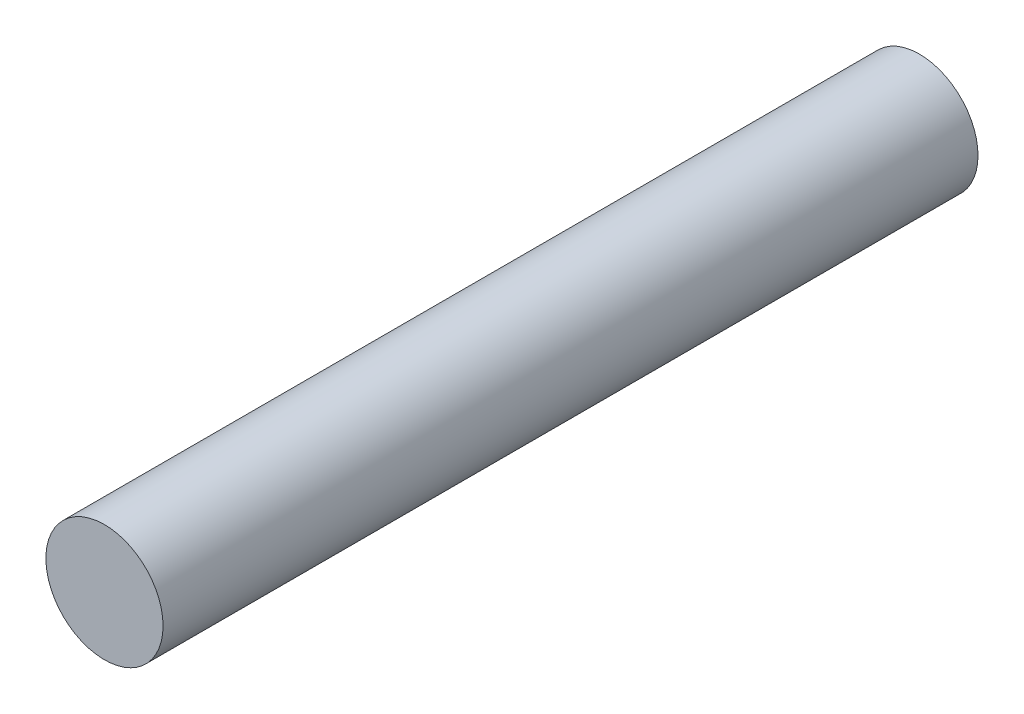
SolidWorks part; units mm, degrees
material "Chrome Stainless Steel"
ref_plane "Front Plane" through (0, 0, 0) normal (0, 0, 1) x (1, 0, 0)
ref_plane "Top Plane" through (0, 0, 0) normal (0, 1, 0) x (1, 0, 0)
ref_plane "Right Plane" through (0, 0, 0) normal (1, 0, 0) x (0, 0, -1)
sketch "Sketch1" plane through (0, 0, 0) normal (0, 0, 1) x (1, 0, 0)
  circle A0 centre (0, 0) radius 0.5715
  dimension "D1" = 1.143
extrude "Boss-Extrude1" add sketch "Sketch1" along normal blind 7.9502
